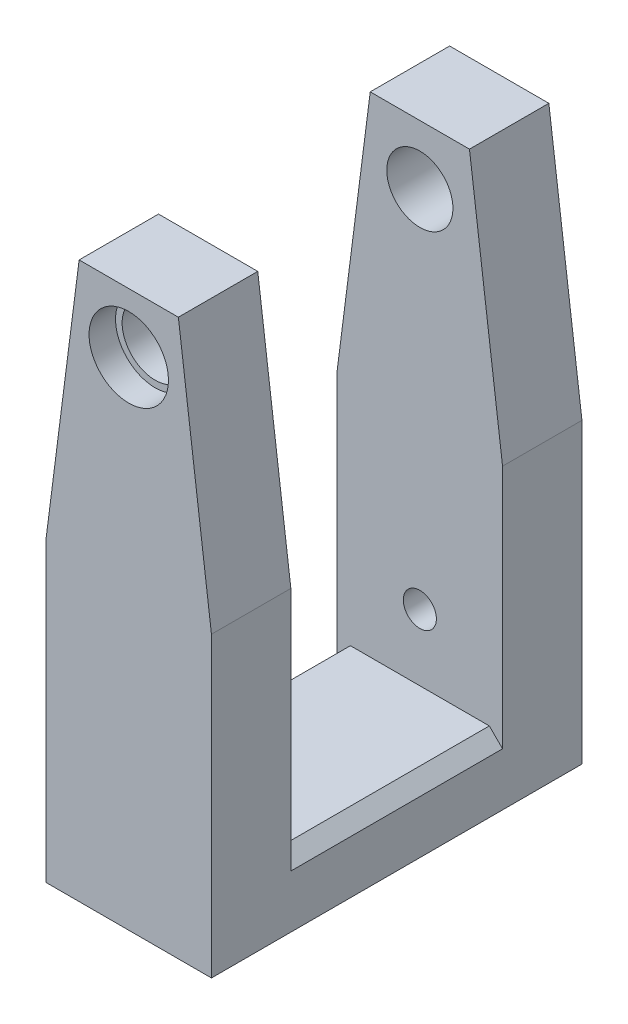
SolidWorks part; units mm, degrees
ref_plane "Front Plane" through (0, 0, 0) normal (0, 0, 1) x (1, 0, 0)
ref_plane "Top Plane" through (0, 0, 0) normal (0, 1, 0) x (1, 0, 0)
ref_plane "Right Plane" through (0, 0, 0) normal (1, 0, 0) x (0, 0, -1)
sketch "Sketch1" plane through (0, 0, 0) normal (0, 0, 1) x (1, 0, 0)
  line L0 (0, 0) -> (0, 168) construction
  line L1 (0, 0) -> (12.5, 0)
  line L2 (-12.5, 0) -> (0, 0)
  line L3 (-12.5, 0) -> (-12.5, 45)
  line L4 (-12.5, 45) -> (-7.5, 84)
  line L5 (-7.5, 84) -> (7.5, 84)
  line L6 (7.5, 84) -> (12.5, 45)
  line L7 (12.5, 45) -> (12.5, 0)
  point P5 (0, 84)
  dimension "D1" = 12.5
  dimension "D2" = 12.5
  dimension "D3" = 45
  dimension "D4" = 45
  dimension "D5" = 84
  dimension "D6" = 15
extrude "Boss-Extrude1" add sketch "Sketch1" along normal blind 56
sketch "Sketch2" plane through (12.5, 0, 0) normal (1, 0, 0) x (0, 0, -1)
  line L0 (-56, 84) -> (0, 84) construction
  line L1 (-44, 84) -> (-12, 84)
  line L2 (-44, 84) -> (-44, 10)
  line L3 (-44, 10) -> (-12, 10)
  line L4 (-12, 84) -> (-12, 10)
  line L5 (-56, 0) -> (0, 0) construction
  point P6 (0, 0)
  dimension "D1" = 32
  dimension "D2" = 12
  dimension "D3" = 12
  dimension "D4" = 10
extrude "Cut-Extrude1" cut sketch "Sketch2" against normal blind 56
chamfer "Chamfer1" distance 2 angle 45 2 edges at (-12.5, 10, 28) (12.5, 10, 28)
sketch "Sketch3" plane through (0, 0, 56) normal (0, 0, 1) x (1, 0, 0)
  line L0 (0, 75) -> (0, 0) construction
  point P0 (0, 75)
  dimension "D1" = 75
hole_wizard "CBORE for M6 Hex Head Bolt1" positions "Sketch3" profile "Sketch7" counterbore size "M6" standard "ISO"
sketch "Sketch7" plane through (0, 75, 56) normal (1, 0, 0) x (0, -1, 0)
  line L0 (0, 0) -> (0, 23.0043)
  line L1 (0, 23.0043) -> (5, 20)
  line L2 (5, 20) -> (5, 4)
  line L3 (5, 4) -> (6, 4)
  line L4 (6, 4) -> (6, 0)
  line L5 (6, 0) -> (0, 0)
  line L10 (0, 23.0043) -> (-5, 20) construction
  line L11 (0, -6.35) -> (0, 107.95) construction
  dimension "Hole Dia." = 10
  dimension "Hole Depth" = 20
  dimension "C'Bore Dia." = 12
  dimension "C'Bore Depth" = 4
  dimension "Drill Angle" = 118
sketch "Sketch11" plane through (0, 0, 0) normal (0, 0, -1) x (-1, 0, 0)
  line L0 (0, 0) -> (0, 75) construction
  point P1 (0, 75)
  dimension "D1" = 75
hole_wizard "CBORE for M6 Hex Head Bolt3" positions "Sketch11" profile "Sketch12" counterbore size "M6" standard "ISO"
sketch "Sketch12" plane through (0, 75, 0) normal (1, 0, 0) x (0, 1, 0)
  line L0 (0, 0) -> (0, 23.0043)
  line L1 (0, 23.0043) -> (5, 20)
  line L2 (5, 20) -> (5, 4)
  line L3 (5, 4) -> (6, 4)
  line L4 (6, 4) -> (6, 0)
  line L5 (6, 0) -> (0, 0)
  line L10 (0, 23.0043) -> (-5, 20) construction
  line L11 (0, -6.35) -> (0, 107.95) construction
  dimension "Hole Dia." = 10
  dimension "Hole Depth" = 20
  dimension "C'Bore Dia." = 12
  dimension "C'Bore Depth" = 4
  dimension "Drill Angle" = 118
sketch "Sketch13" plane through (0, 0, 0) normal (0, 0, -1) x (-1, 0, 0)
  line L0 (0, 0) -> (0, 20) construction
  point P1 (0, 20)
  dimension "D1" = 20
hole_wizard "M6x1.0 Tapped Hole1" positions "3DSketch5" profile "Sketch17" tap size "M6x1.0" standard "ANSI Metric"
sketch3d "3DSketch5"
  point P0 (0, 20, 0)
sketch "Sketch17" plane through (0, 20, 0) normal (1, 0, 0) x (0, 1, 0)
  line L0 (0, 0) -> (0, 28.5022)
  line L1 (0, 28.5022) -> (2.5, 27)
  line L2 (2.5, 27) -> (2.5, 0)
  line L5 (2.5, 0) -> (0, 0)
  line L10 (0, 28.5022) -> (-2.5, 27) construction
  line L11 (0, -6.35) -> (0, 107.95) construction
  dimension "Tap Drill Dia." = 5
  dimension "Tap Drill Depth" = 27
  dimension "Drill Angle" = 118
cosmetic thread "Hole Thread2" parameters "D1"=22, "D2"=6
